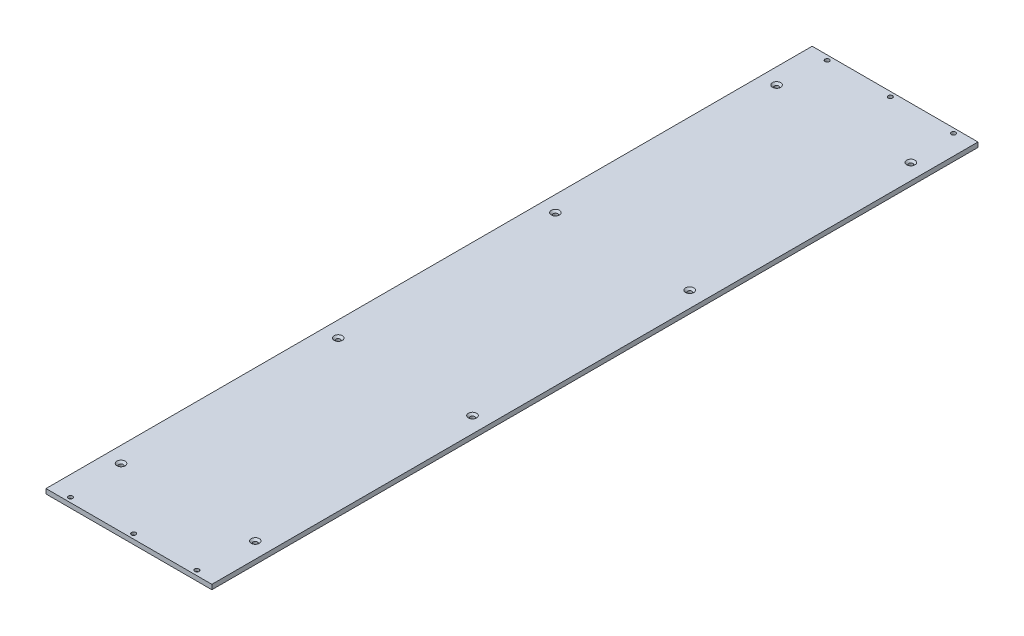
SolidWorks part; units mm, degrees
ref_plane "Front Plane" through (0, 0, 0) normal (0, 0, 1) x (1, 0, 0)
ref_plane "Top Plane" through (0, 0, 0) normal (0, 1, 0) x (1, 0, 0)
ref_plane "Right Plane" through (0, 0, 0) normal (1, 0, 0) x (0, 0, -1)
sketch "Sketch1" plane through (0, 0, 0) normal (0, 1, 0) x (1, 0, 0)
  line L1 (0, 0) -> (210, 0)
  line L2 (0, 0) -> (0, 970)
  line L3 (0, 970) -> (210, 970)
  line L4 (210, 0) -> (210, 970)
  dimension "D1" = 210
  dimension "D2" = 970
extrude "Boss-Extrude1" add sketch "Sketch1" along normal blind 6
hole_wizard "CSK for M5 Flat Head Machine Screw1" positions "Sketch3" profile "Sketch2" countersink size "M5" standard "ANSI Metric" end condition through all
sketch "Sketch3" plane through (0, 6, 0) normal (0, 1, 0) x (1, 0, 0)
  line L0 (0, 0) -> (210, 0) construction
  line L2 (0, 970) -> (0, 0) construction
  point P0 (20, 75)
  point P9 (0, 86.7877)
  dimension "D1" = 75
  dimension "D2" = 20
sketch "Sketch2" plane through (20, 6, -75) normal (1, 0, 0) x (0, 0, 1)
  line L0 (0, 0) -> (0, 6)
  line L1 (0, 6) -> (2.75, 6)
  line L2 (2.75, 6) -> (2.75, 2.45)
  line L3 (2.75, 2.45) -> (5.2, 0)
  line L5 (5.2, 0) -> (0, 0)
  line L6 (-2.75, 2.45) -> (-5.2, 0) construction
  line L11 (0, -6.35) -> (0, 107.95) construction
  dimension "Thru Hole Dia." = 5.5
  dimension "Thru Hole Depth" = 6
  dimension "Near C'Sink Dia." = 10.4
  dimension "Near C'Sink Angle" = 90
pattern_linear "LPattern1" count 3 spacing 275 along (0, 0, -1) of "CSK for M5 Flat Head Machine Screw1"
pattern_linear "LPattern2" count 2 spacing 830 along (0, 0, -1) of "CSK for M5 Flat Head Machine Screw1"
sketch "Sketch4" plane through (0, 6, 0) normal (0, 1, 0) x (1, 0, 0)
  line L0 (105, 970) -> (105, 0)
  line L1 (210, 970) -> (0, 970) construction
  line L2 (0, 0) -> (210, 0) construction
sketch "Sketch5" plane through (0, 0, 0) normal (0, 0, 1) x (1, 0, 0)
  line L0 (105, 6) -> (105, 0) construction
  line L1 (0, 6) -> (210, 6) construction
  line L2 (0, 0) -> (210, 0) construction
ref_plane "Plane1" through (105, 0, 0) normal (1, 0, 0) x (0, 0, -1)
mirror "Mirror1" about plane through (105, 0, 0) normal (1, 0, 0) of "LPattern2", "LPattern1", "CSK for M5 Flat Head Machine Screw1"
hole_wizard "CSK for M5 Flat Head Machine Screw2" positions "Sketch7" profile "Sketch6" countersink size "M5" standard "ANSI Metric" end condition through all
sketch "Sketch7" plane through (0, 0, 0) normal (0, -1, 0) x (-1, 0, 0)
  line L0 (0, 0) -> (-210, 0) construction
  line L2 (0, 970) -> (0, 0) construction
  line L3 (-210, 0) -> (-210, 970) construction
  point P0 (-25, 6)
  point P14 (-185, 6)
  point P16 (-105, 6)
  dimension "D1" = 6
  dimension "D2" = 25
  dimension "D3" = 25
  dimension "D4" = 105
sketch "Sketch6" plane through (25, 0, -6) normal (1, 0, 0) x (0, 0, -1)
  line L0 (0, 0) -> (0, 6)
  line L1 (0, 6) -> (2.75, 6)
  line L2 (2.75, 6) -> (2.75, 2.45)
  line L3 (2.75, 2.45) -> (5.2, 0)
  line L5 (5.2, 0) -> (0, 0)
  line L6 (-2.75, 2.45) -> (-5.2, 0) construction
  line L11 (0, -6.35) -> (0, 107.95) construction
  dimension "Thru Hole Dia." = 5.5
  dimension "Thru Hole Depth" = 6
  dimension "Near C'Sink Dia." = 10.4
  dimension "Near C'Sink Angle" = 90
sketch "Sketch8" plane through (0, 6, 0) normal (0, 1, 0) x (1, 0, 0)
  line L0 (0, 485) -> (210, 485) construction
  line L1 (0, 970) -> (0, 0) construction
  line L2 (210, 0) -> (210, 970) construction
sketch "Sketch9" plane through (210, 0, 0) normal (1, 0, 0) x (0, 0, -1)
  line L0 (485, 6) -> (485, 0) construction
  line L1 (0, 0) -> (970, 0) construction
ref_plane "Plane2" through (0, 0, -485) normal (0, 0, -1) x (-1, 0, 0)
mirror "Mirror2" about plane through (0, 0, -485) normal (0, 0, -1) of "CSK for M5 Flat Head Machine Screw2"
